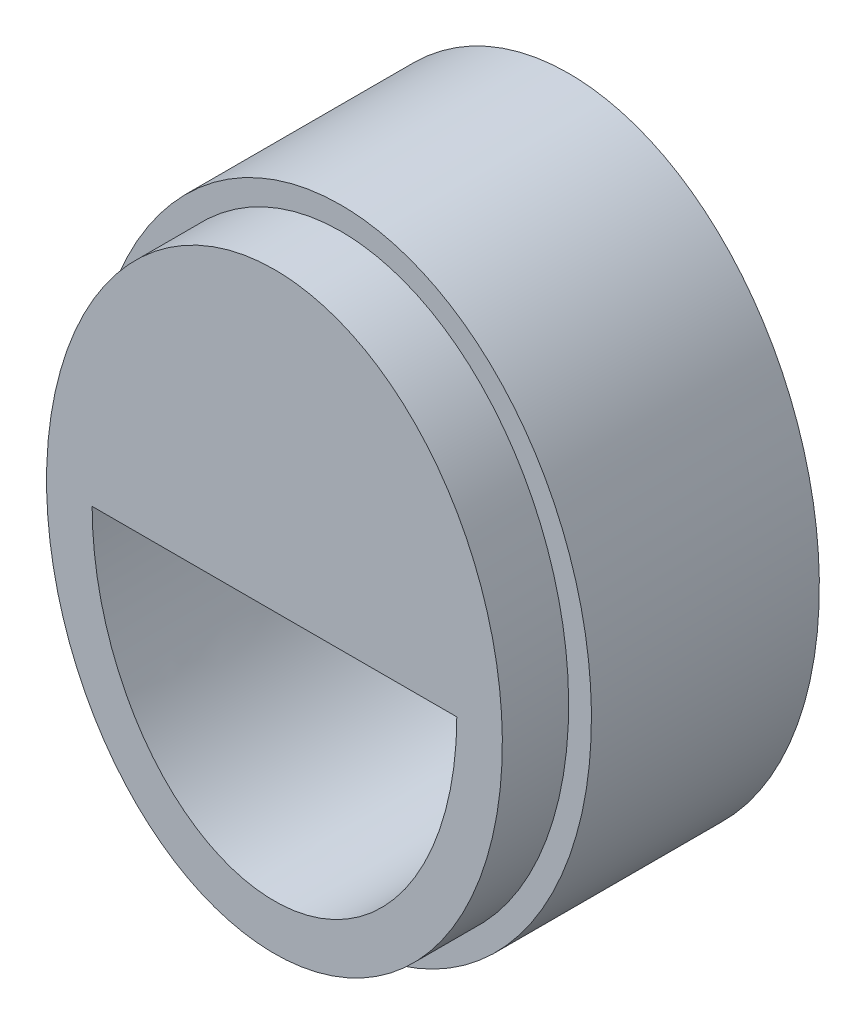
SolidWorks part; units mm, degrees
ref_plane "Alzado" through (0, 0, 0) normal (0, 0, 1) x (1, 0, 0)
ref_plane "Planta" through (0, 0, 0) normal (0, 1, 0) x (1, 0, 0)
ref_plane "Vista lateral" through (0, 0, 0) normal (1, 0, 0) x (0, 0, -1)
sketch "Croquis1" plane through (0, 0, 0) normal (0, 0, 1) x (1, 0, 0)
  ellipse E0 centre (0, 0) end of major axis (0, 14) minor radius 11
  ellipse E1 centre (0, 0) end of major axis (0, 12) minor radius 9
extrude "Saliente-Extruir1" add sketch "Croquis1" along normal blind 10
sketch "Croquis2" plane through (0, 0, 10) normal (0, 0, 1) x (1, 0, 0)
  ellipse E0 centre (0, 0) end of major axis (0, 13) minor radius 10
  ellipse E2 centre (0, 0) end of major axis (0, 11) minor radius 8
extrude "Saliente-Extruir3" add sketch "Croquis2" along normal blind 2.9097 and the other way blind 8
sketch "Croquis4" plane through (0, 0, 12.9097) normal (0, 0, 1) x (1, 0, 0)
  line L0 (-8, 0) -> (8, 0)
  ellipse E0 centre (0, 0) end of major axis (0, 11) minor radius 8 (8, 0) -> (-8, 0) ccw
  ellipse E1 centre (0, 0) end of major axis (0, 11) minor radius 8 construction
extrude "Saliente-Extruir4" add sketch "Croquis4" against normal blind 2
